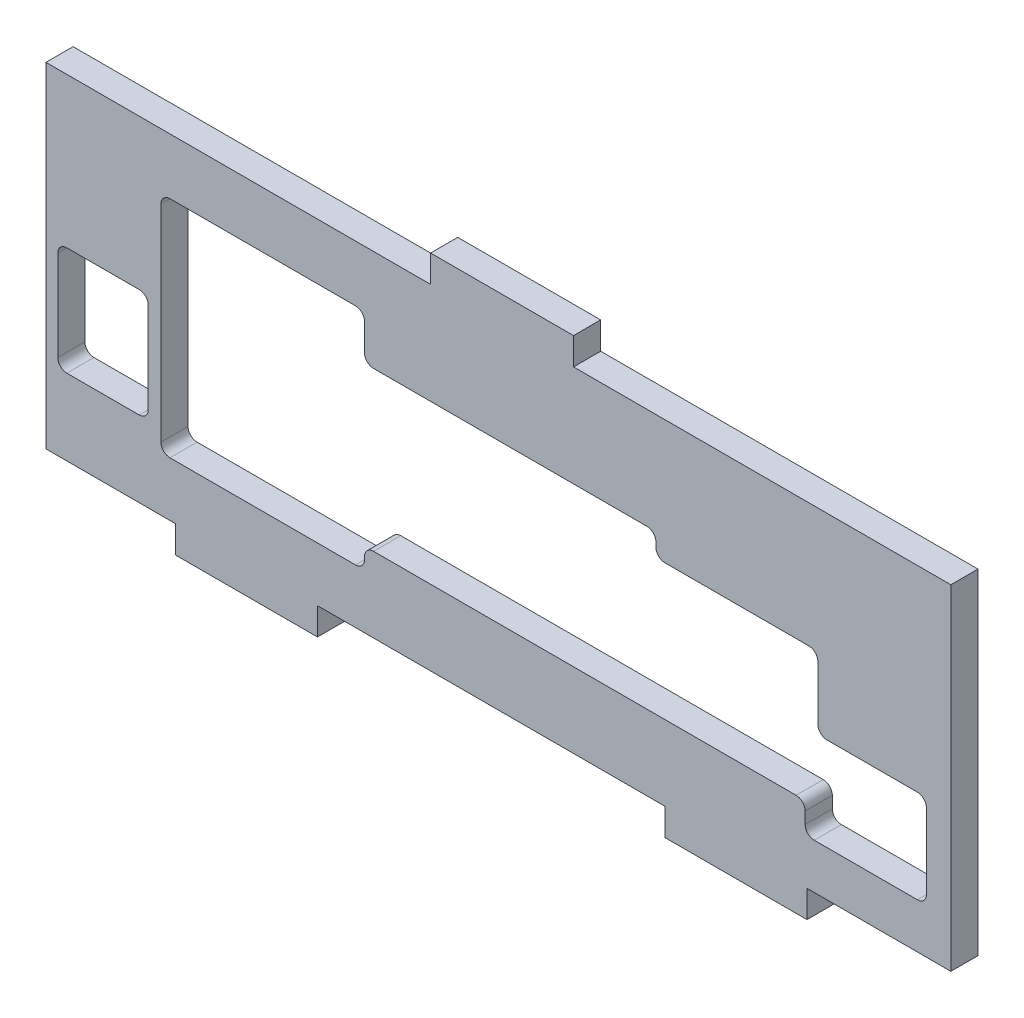
SolidWorks part; units mm, degrees
ref_plane "Alzado" through (0, 0, 0) normal (0, 0, 1) x (1, 0, 0)
ref_plane "Planta" through (0, 0, 0) normal (0, 1, 0) x (1, 0, 0)
ref_plane "Vista lateral" through (0, 0, 0) normal (1, 0, 0) x (0, 0, -1)
sketch "Croquis1" plane through (0, 0, 0) normal (0, 0, 1) x (1, 0, 0)
  line L0 (-14.8, -11.2) -> (-14.8, -11.5)
  line L1 (-50, 21.5) -> (50, 21.5)
  line L2 (-50, 21.5) -> (-50, -21.5)
  line L3 (-50, -21.5) -> (50, -21.5)
  line L4 (50, 21.5) -> (50, -21.5)
  line L5 (-50, 21.5) -> (50, -21.5) construction
  line L6 (-50, -21.5) -> (50, 21.5) construction
  line L7 (50, 21.5) -> (8.3, 21.5)
  line L8 (50, 21.5) -> (50, 18.5)
  line L9 (50, 18.5) -> (8.3, 18.5)
  line L10 (8.3, 21.5) -> (8.3, 18.5)
  line L11 (-50, 21.5) -> (-7.5, 21.5)
  line L12 (-50, 21.5) -> (-50, 18.5)
  line L13 (-50, 18.5) -> (-7.5, 18.5)
  line L14 (-7.5, 21.5) -> (-7.5, 18.5)
  line L15 (-50, -21.5) -> (-35.7, -21.5)
  line L16 (-50, -21.5) -> (-50, -18.5)
  line L17 (-50, -18.5) -> (-35.7, -18.5)
  line L18 (-35.7, -21.5) -> (-35.7, -18.5)
  line L19 (-20, -21.5) -> (18.4, -21.5)
  line L20 (-20, -21.5) -> (-20, -18.5)
  line L21 (-20, -18.5) -> (18.4, -18.5)
  line L22 (18.4, -21.5) -> (18.4, -18.5)
  line L23 (50, -21.5) -> (34.1, -21.5)
  line L24 (50, -21.5) -> (50, -18.5)
  line L25 (50, -18.5) -> (34.1, -18.5)
  line L26 (34.1, -21.5) -> (34.1, -18.5)
  line L27 (-47.7, 1.9) -> (-39.7, 1.9)
  line L28 (-48.7, 0.9) -> (-48.7, -9.1)
  line L29 (-47.7, -10.1) -> (-39.7, -10.1)
  line L30 (-38.7, 0.9) -> (-38.7, -9.1)
  line L31 (-36.3, 12.3) -> (-15.8, 12.3)
  line L32 (-37.3, 11.3) -> (-37.3, -11.5)
  line L33 (-36.3, -12.5) -> (-15.8, -12.5)
  line L34 (-14.8, 11.3) -> (-14.8, 8.3)
  line L35 (-13.8, 7.3) -> (16.4, 7.3)
  line L37 (-13.8, -10.2) -> (17.4, -10.2)
  line L38 (17.4, 6.3) -> (17.4, 5.8)
  line L39 (34.3, 4.8) -> (18.4, 4.8)
  line L40 (35.3, 3.8) -> (35.3, -2.2)
  line L41 (32.9, -10.2) -> (17.4, -10.2)
  line L43 (46.3, -3.2) -> (36.3, -3.2)
  line L44 (47.3, -4.2) -> (47.3, -12.5)
  line L45 (46.3, -13.5) -> (34.9, -13.5)
  line L46 (33.9, -11.2) -> (33.9, -12.5)
  arc A0 (-39.7, -10.1) -> (-38.7, -9.1) centre (-39.7, -9.1) ccw
  arc A1 (-38.7, 0.9) -> (-39.7, 1.9) centre (-39.7, 0.9) ccw
  arc A2 (-47.7, -10.1) -> (-48.7, -9.1) centre (-47.7, -9.1) cw
  arc A3 (-48.7, 0.9) -> (-47.7, 1.9) centre (-47.7, 0.9) cw
  arc A4 (47.3, -12.5) -> (46.3, -13.5) centre (46.3, -12.5) cw
  arc A5 (34.9, -13.5) -> (33.9, -12.5) centre (34.9, -12.5) cw
  arc A6 (47.3, -4.2) -> (46.3, -3.2) centre (46.3, -4.2) ccw
  arc A7 (36.3, -3.2) -> (35.3, -2.2) centre (36.3, -2.2) cw
  arc A8 (33.9, -11.2) -> (32.9, -10.2) centre (32.9, -11.2) ccw
  arc A9 (35.3, 3.8) -> (34.3, 4.8) centre (34.3, 3.8) ccw
  arc A10 (18.4, 4.8) -> (17.4, 5.8) centre (18.4, 5.8) cw
  arc A11 (17.4, 6.3) -> (16.4, 7.3) centre (16.4, 6.3) ccw
  arc A12 (-13.8, 7.3) -> (-14.8, 8.3) centre (-13.8, 8.3) cw
  arc A13 (-14.8, 11.3) -> (-15.8, 12.3) centre (-15.8, 11.3) ccw
  arc A14 (-14.8, -11.2) -> (-13.8, -10.2) centre (-13.8, -11.2) cw
  arc A15 (-14.8, -11.5) -> (-15.8, -12.5) centre (-15.8, -11.5) cw
  arc A16 (-36.3, -12.5) -> (-37.3, -11.5) centre (-36.3, -11.5) cw
  arc A17 (-37.3, 11.3) -> (-36.3, 12.3) centre (-36.3, 11.3) cw
  point P0 (0, 0)
  dimension "D13" = 1
  dimension "D17" = 1
  dimension "D1" = 100
  dimension "D2" = 43
  dimension "D3" = 15.9
  dimension "D4" = 15.7
  dimension "D5" = 38.4
  dimension "D6" = 15.7
  dimension "D7" = 3
  dimension "D8" = 3
  dimension "D9" = 41.7
  dimension "D10" = 15.8
  dimension "D11" = 24.8
  dimension "D12" = 22.5
  dimension "D14" = 17.5
  dimension "D15" = 15
  dimension "D16" = 10.3
  dimension "D18" = 12
  dimension "D19" = 10
  dimension "D20" = 1.3
  dimension "D21" = 8.4
  dimension "D22" = 9
  dimension "D23" = 12.7
  dimension "D24" = 5
  dimension "D25" = 13.4
  dimension "D26" = 5
  dimension "D27" = 72.6
  dimension "D28" = 17.9
  dimension "D29" = 12
  dimension "D30" = 37
extrude "Saliente-Extruir1" add sketch "Croquis1" along normal blind 3 contours L3 L26 L25 L4 L9 L10 L1 L14 L13 L2 L17 L18 L20 L21 L22
